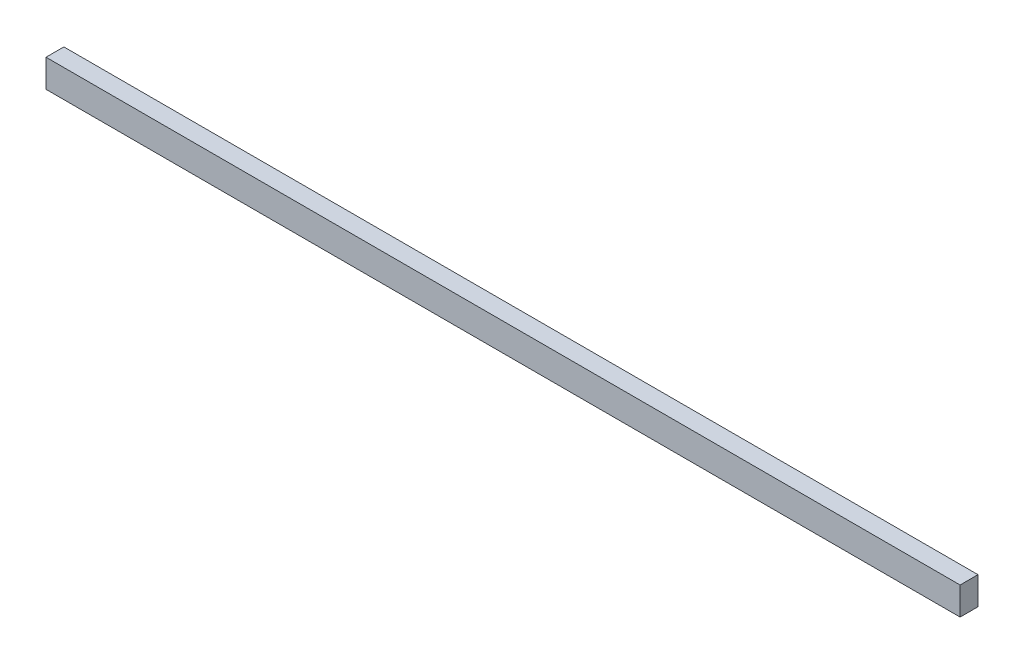
SolidWorks part; units mm, degrees
material "Pine"
ref_plane "Front Plane" through (0, 0, 0) normal (0, 0, 1) x (1, 0, 0)
ref_plane "Top Plane" through (0, 0, 0) normal (0, 1, 0) x (1, 0, 0)
ref_plane "Right Plane" through (0, 0, 0) normal (1, 0, 0) x (0, 0, -1)
sketch "Sketch1" plane through (0, 0, 0) normal (1, 0, 0) x (0, 0, -1)
  line L1 (0, 0) -> (45, 0)
  line L2 (0, 0) -> (0, -70)
  line L3 (0, -70) -> (45, -70)
  line L4 (45, 0) -> (45, -70)
  dimension "D1" = 70
  dimension "D2" = 45
extrude "Boss-Extrude1" add sketch "Sketch1" along normal blind 2300
